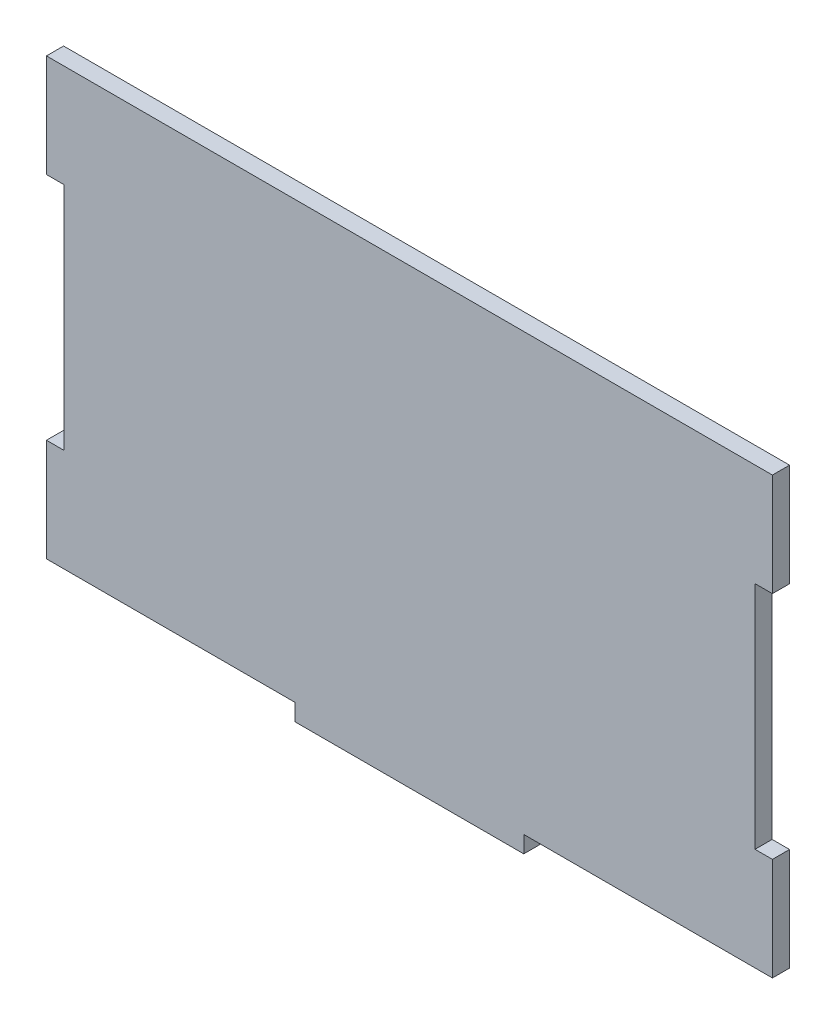
SolidWorks part; units mm, degrees
ref_plane "Front Plane" through (0, 0, 0) normal (0, 0, 1) x (1, 0, 0)
ref_plane "Top Plane" through (0, 0, 0) normal (0, 1, 0) x (1, 0, 0)
ref_plane "Right Plane" through (0, 0, 0) normal (1, 0, 0) x (0, 0, -1)
sketch "Sketch1" plane through (0, 0, 0) normal (0, 0, 1) x (1, 0, 0)
  line L1 (-63.5, -38.1) -> (63.5, -38.1)
  line L2 (-63.5, -38.1) -> (-63.5, 38.1)
  line L3 (-63.5, 38.1) -> (63.5, 38.1)
  line L4 (63.5, -38.1) -> (63.5, 38.1)
  line L5 (-63.5, -38.1) -> (63.5, 38.1) construction
  line L6 (-63.5, 38.1) -> (63.5, -38.1) construction
  point P0 (0, 0)
  dimension "D1" = 127
  dimension "D2" = 76.2
extrude "Boss-Extrude1" add sketch "Sketch1" along normal mid plane 2.9972
sketch "Sketch2" plane through (0, 0, 1.4986) normal (0, 0, 1) x (1, 0, 0)
  line L0 (-63.5, 38.1) -> (-63.5, -38.1) construction
  line L1 (-63.5, 20.127) -> (-60.452, 20.127)
  line L2 (-63.5, 20.127) -> (-63.5, -20.127)
  line L3 (-63.5, -20.127) -> (-60.452, -20.127)
  line L4 (-60.452, 20.127) -> (-60.452, -20.127)
  line L5 (-63.5, 0) -> (0, 0) construction
  line L6 (0, 0) -> (0, 38.1) construction
  line L7 (63.5, 38.1) -> (-63.5, 38.1) construction
  line L8 (60.452, 20.127) -> (60.452, -20.127)
  line L9 (63.5, -20.127) -> (60.452, -20.127)
  line L10 (63.5, 20.127) -> (63.5, -20.127)
  line L11 (63.5, 20.127) -> (60.452, 20.127)
  line L13 (-63.5, -38.1) -> (63.5, -38.1) construction
  line L14 (-20.127, -38.1) -> (20.127, -38.1)
  line L15 (-20.127, -38.1) -> (-20.127, -41.0464)
  line L16 (-20.127, -41.0464) -> (20.127, -41.0464)
  line L17 (20.127, -38.1) -> (20.127, -41.0464)
  point P22 (0, -38.1)
  dimension "D1" = 40.254
  dimension "D2" = 3.048
  dimension "D3" = 40.254
  dimension "D4" = 2.9464
extrude "Cut-Extrude1" cut sketch "Sketch2" against normal through all
sketch "Sketch3" plane through (0, 0, 1.4986) normal (0, 0, 1) x (1, 0, 0)
  line L0 (-63.5, -38.1) -> (63.5, -38.1) construction
  line L1 (-20, -38.1) -> (20, -38.1)
  line L2 (-20, -38.1) -> (-20, -41.0464)
  line L3 (-20, -41.0464) -> (20, -41.0464)
  line L4 (20, -38.1) -> (20, -41.0464)
  point P6 (0, -38.1)
  dimension "D1" = 40
  dimension "D2" = 2.9464
extrude "Boss-Extrude2" add sketch "Sketch3" against normal through all
